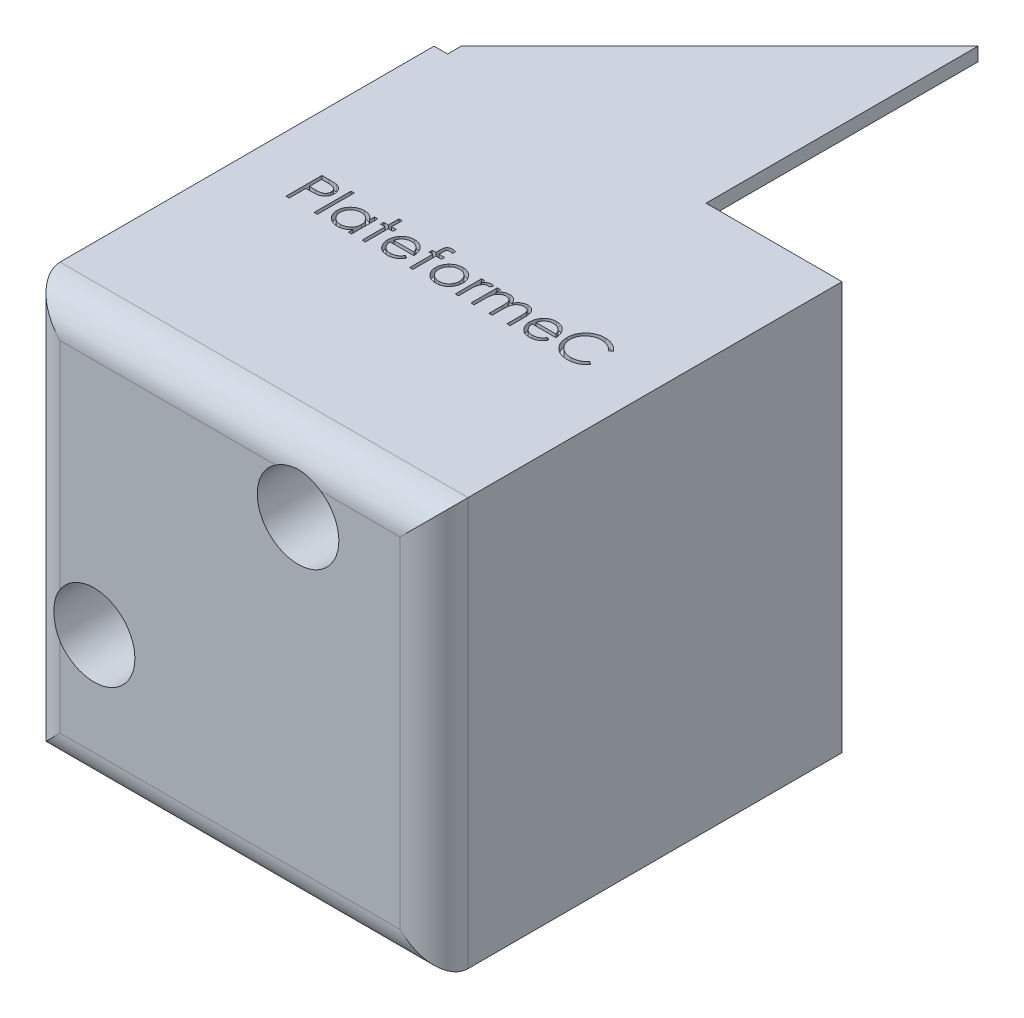
SolidWorks part; units mm, degrees
ref_plane "Plan de face" through (0, 0, 0) normal (0, 0, 1) x (1, 0, 0)
ref_plane "Plan de dessus" through (0, 0, 0) normal (0, 1, 0) x (1, 0, 0)
ref_plane "Plan de droite" through (0, 0, 0) normal (1, 0, 0) x (0, 0, -1)
sketch "Esquisse1" plane through (0, 0, 0) normal (0, 0, 1) x (1, 0, 0)
  line L1 (0, 0) -> (-60, 0)
  line L2 (0, 0) -> (0, 60)
  line L3 (0, 60) -> (-60, 60)
  line L4 (-60, 0) -> (-60, 60)
  dimension "D1" = 60
  dimension "D2" = 60
extrude "Boss.-Extru.1" add sketch "Esquisse1" along normal blind 60
sketch "Esquisse3" plane through (0, 0, 0) normal (0, 0, -1) x (-1, 0, 0)
  line L0 (60, 60) -> (60, 20)
  line L1 (60, 60) -> (60, 0) construction
  line L2 (60, 20) -> (58, 20)
  line L3 (58, 20) -> (58, 58)
  line L4 (58, 58) -> (20, 58)
  line L5 (20, 58) -> (20, 60)
  line L6 (0, 60) -> (60, 60) construction
  line L7 (20, 60) -> (60, 60)
  dimension "D1" = 40
  dimension "D2" = 40
  dimension "D3" = 2
  dimension "D4" = 2
extrude "Boss.-Extru.3" add sketch "Esquisse3" along normal blind 40
sketch "Esquisse6" plane through (-60, 0, 0) normal (-1, 0, 0) x (0, 0, 1)
  line L0 (30, 0) -> (30, 60) construction
  line L1 (60, 0) -> (0, 0) construction
  line L2 (60, 60) -> (-40, 60) construction
  text T0 "PING" font "Century Gothic" height in points 48
extrude "Enlèv. mat.-Extru.3" cut sketch "Esquisse6" against normal blind 1
sketch "Esquisse7" plane through (0, 60, 0) normal (0, 1, 0) x (1, 0, 0)
  line L0 (0, -30) -> (-60, -30) construction
  line L1 (0, -60) -> (0, 0) construction
  line L2 (-60, -60) -> (-60, 40) construction
  text T0 "PlateformeC" font "Century Gothic" height in points 20
extrude "Enlèv. mat.-Extru.4" cut sketch "Esquisse7" against normal blind 1
sketch "Esquisse8" plane through (-60, 0, 0) normal (-1, 0, 0) x (0, 0, 1)
  line L0 (-40, 20) -> (0, 60)
  line L1 (60, 60) -> (-40, 60) construction
  line L2 (0, 60) -> (-40, 60)
  line L3 (-40, 60) -> (-40, 20)
  dimension "D1" = 45
extrude "Enlèv. mat.-Extru.5" cut sketch "Esquisse8" against normal blind 2
sketch "Esquisse11" plane through (0, 60, 0) normal (0, 1, 0) x (1, 0, 0)
  line L0 (-20, 40) -> (-60, 0)
  line L1 (-60, 0) -> (-61.461, 41.461)
  line L2 (-61.461, 41.461) -> (-20, 40)
extrude "Enlèv. mat.-Extru.6" cut sketch "Esquisse11" against normal blind 2
fillet "Congé1" radius 5 4 edges at (-30, 0, 60) (0, 30, 60) (-60, 30, 60) (-30, 60, 60)
sketch "Esquisse13" plane through (0, 0, 60) normal (0, 0, 1) x (1, 0, 0)
  line L0 (-60, 60) -> (0, 60) construction
  line L1 (-60, 0) -> (-60, 60) construction
  circle A0 centre (-50, 20) radius 3
  circle A1 centre (-20, 50) radius 3
  dimension "D1" = 6
  dimension "D2" = 6
  dimension "D3" = 10
  dimension "D4" = 10
  dimension "D5" = 40
  dimension "D6" = 40
extrude "Enlèv. mat.-Extru.7" cut sketch "Esquisse13" against normal through all
sketch "Esquisse14" plane through (0, 0, 60) normal (0, 0, 1) x (1, 0, 0)
  circle A0 centre (-50, 20) radius 6
  circle A1 centre (-20, 50) radius 6
  dimension "D1" = 12
  dimension "D2" = 12
extrude "Enlèv. mat.-Extru.8" cut sketch "Esquisse14" against normal blind 54
